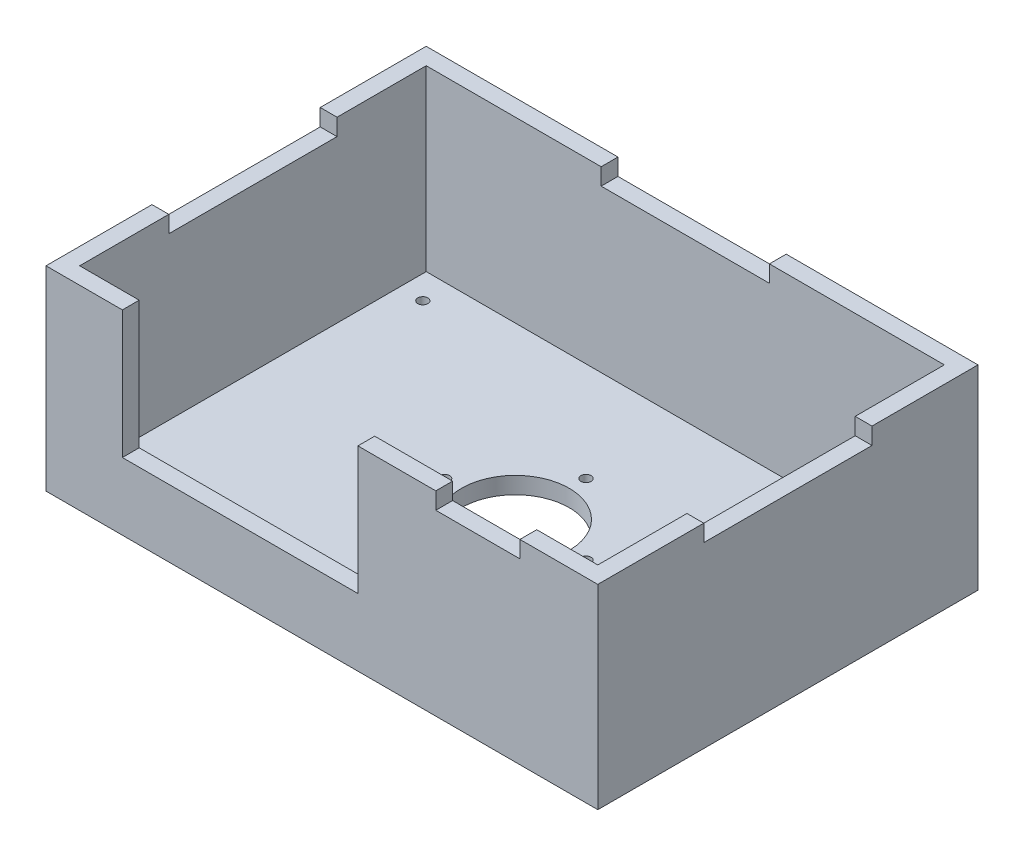
SolidWorks part; units mm, degrees
ref_plane "Front Plane" through (0, 0, 0) normal (0, 0, 1) x (1, 0, 0)
ref_plane "Top Plane" through (0, 0, 0) normal (0, 1, 0) x (1, 0, 0)
ref_plane "Right Plane" through (0, 0, 0) normal (1, 0, 0) x (0, 0, -1)
sketch "Esquisse1" plane through (0, 0, 0) normal (0, 1, 0) x (1, 0, 0)
  line L1 (-77, -50.5) -> (77, -50.5)
  line L2 (-77, -50.5) -> (-77, 50.5)
  line L3 (-77, 50.5) -> (77, 50.5)
  line L4 (77, -50.5) -> (77, 50.5)
  line L5 (-77, -50.5) -> (77, 50.5) construction
  line L6 (-77, 50.5) -> (77, -50.5) construction
  point P0 (0, 0)
  dimension "D1" = 154
  dimension "D2" = 101
extrude "Boss.-Extru.1" add sketch "Esquisse1" along normal blind 5
sketch "Esquisse2" plane through (0, 5, 0) normal (0, 1, 0) x (1, 0, 0)
  circle A0 centre (0, 0) radius 16
  circle A5 centre (0, 0) radius 21
  circle A6 centre (21, 0) radius 1.5
  circle A7 centre (0, 21) radius 1.5
  circle A8 centre (-21, 0) radius 1.5
  circle A9 centre (0, -21) radius 1.5
  dimension "D1" = 32
  dimension "D2" = 42
  dimension "D3" = 3
  dimension "D4" = 3
  dimension "D5" = 3
  dimension "D6" = 3
extrude "Enlèv. mat.-Extru.2" cut sketch "Esquisse2" against normal blind 5 contours A0 | A7 | A8 | A6 | A9
sketch "Esquisse3" plane through (0, 5, 0) normal (0, 1, 0) x (1, 0, 0)
  line L0 (77, -50.5) -> (77, 50.5) construction
  line L1 (-77, -50.5) -> (77, -50.5) construction
  line L2 (-77, 50.5) -> (-77, -50.5) construction
  line L3 (77, 50.5) -> (-77, 50.5) construction
  circle A0 centre (70, -45.5) radius 1.5
  circle A1 centre (-70, -45.5) radius 1.5
  circle A2 centre (-70, 42.5) radius 1.5
  circle A3 centre (70, 42.5) radius 1.5
  point P14 (-54.4083, -50.105)
  point P17 (0, 0)
  point P18 (0, 0)
  point P19 (0, 0)
  point P20 (0, 0)
  point P21 (0, 0)
  dimension "D1" = 3
  dimension "D2" = 3
  dimension "D3" = 3
  dimension "D4" = 3
  dimension "D5" = 7
  dimension "D6" = 5
  dimension "D7" = 7
  dimension "D8" = 88
  dimension "D9" = 7
  dimension "D10" = 8
  dimension "D11" = 8
  dimension "D12" = 140
  dimension "D13" = 5
  dimension "D14" = 7
extrude "Enlèv. mat.-Extru.3" cut sketch "Esquisse3" against normal blind 5
sketch "Esquisse8" plane through (0, 5, 0) normal (0, 1, 0) x (1, 0, 0)
  line L0 (77, 50.5) -> (-77, 50.5) construction
  line L1 (-82, 55.5) -> (82, 55.5)
  line L2 (-82, 55.5) -> (-82, -57.5)
  line L3 (-82, -57.5) -> (82, -57.5)
  line L4 (82, 55.5) -> (82, -57.5)
  line L5 (-77, 50.5) -> (-77, -50.5) construction
  line L6 (77, -50.5) -> (77, 50.5) construction
  line L13 (-77, 50.5) -> (77, 50.5)
  line L14 (80.0495, 50.5) -> (-77, -48.5762) construction
  line L15 (-77, 50.5) -> (-77, -52.5)
  line L16 (-77, -52.5) -> (77, -52.5)
  line L17 (77, 50.5) -> (77, -52.5)
  point P12 (0, 0)
  dimension "D1" = 5
  dimension "D2" = 5
  dimension "D3" = 5
  dimension "D4" = 5
  dimension "D5" = 103
extrude "Boss.-Extru.3" add sketch "Esquisse8" along normal blind 53 and the other way blind 5 separate body
sketch "Esquisse9" plane through (0, 0, 0) normal (0, -1, 0) x (-1, 0, 0)
  line L1 (-77, -52.5) -> (77, -52.5)
  line L2 (-77, -52.5) -> (-77, -50.5)
  line L3 (-77, -50.5) -> (77, -50.5)
  line L4 (77, -52.5) -> (77, -50.5)
extrude "Boss.-Extru.4" add sketch "Esquisse9" against normal blind 5
sketch "Esquisse11" plane through (0, 58, 0) normal (0, 1, 0) x (1, 0, 0)
  line L0 (-77, -52.5) -> (77, -52.5) construction
  line L1 (-59.3, -52.5) -> (10.7, -52.5)
  line L2 (-59.3, -52.5) -> (-59.3, -57.5)
  line L3 (-59.3, -57.5) -> (10.7, -57.5)
  line L4 (10.7, -52.5) -> (10.7, -57.5)
  line L5 (-82, -57.5) -> (82, -57.5) construction
  line L6 (-77, 50.5) -> (-77, -52.5) construction
  dimension "D1" = 17.7
  dimension "D2" = 70
extrude "Enlèv. mat.-Extru.7" cut sketch "Esquisse11" against normal blind 38
sketch "Esquisse12" plane through (0, 58, 0) normal (0, 1, 0) x (1, 0, 0)
  line L0 (82, 55.5) -> (-82, 55.5) construction
  line L1 (-25, 55.5) -> (25, 55.5)
  line L2 (-25, 55.5) -> (-25, 50.5)
  line L3 (-25, 50.5) -> (25, 50.5)
  line L4 (25, 55.5) -> (25, 50.5)
  line L5 (77, 50.5) -> (-77, 50.5) construction
  line L6 (77, -52.5) -> (77, 50.5) construction
  line L7 (77, 24) -> (82, 24)
  line L8 (77, 24) -> (77, -26)
  line L9 (77, -26) -> (82, -26)
  line L10 (82, 24) -> (82, -26)
  line L11 (82, -57.5) -> (82, 55.5) construction
  line L12 (-82, 55.5) -> (-82, -57.5) construction
  line L13 (-82, 24) -> (-77, 24)
  line L14 (-82, 24) -> (-82, -26)
  line L15 (-82, -26) -> (-77, -26)
  line L16 (-77, 24) -> (-77, -26)
  line L17 (-77, 50.5) -> (-77, -52.5) construction
  point P24 (-25, 53)
  dimension "D1" = 50
  dimension "D2" = 50
  dimension "D3" = 50
  dimension "D4" = 31.5
  dimension "D5" = 31.5
  dimension "D6" = 57
extrude "Enlèv. mat.-Extru.8" cut sketch "Esquisse12" against normal blind 5
sketch "Esquisse13" plane through (0, 58, 0) normal (0, 1, 0) x (1, 0, 0)
  line L0 (77, -52.5) -> (-77, -52.5) construction
  line L1 (33.85, -52.5) -> (58.85, -52.5)
  line L2 (33.85, -52.5) -> (33.85, -57.5)
  line L3 (33.85, -57.5) -> (58.85, -57.5)
  line L4 (58.85, -52.5) -> (58.85, -57.5)
  line L5 (10.7, -57.5) -> (82, -57.5) construction
  line L6 (10.7, -57.5) -> (10.7, -52.5) construction
  point P8 (33.85, -55)
  dimension "D1" = 25
  dimension "D2" = 23.15
extrude "Enlèv. mat.-Extru.9" cut sketch "Esquisse13" against normal blind 5
